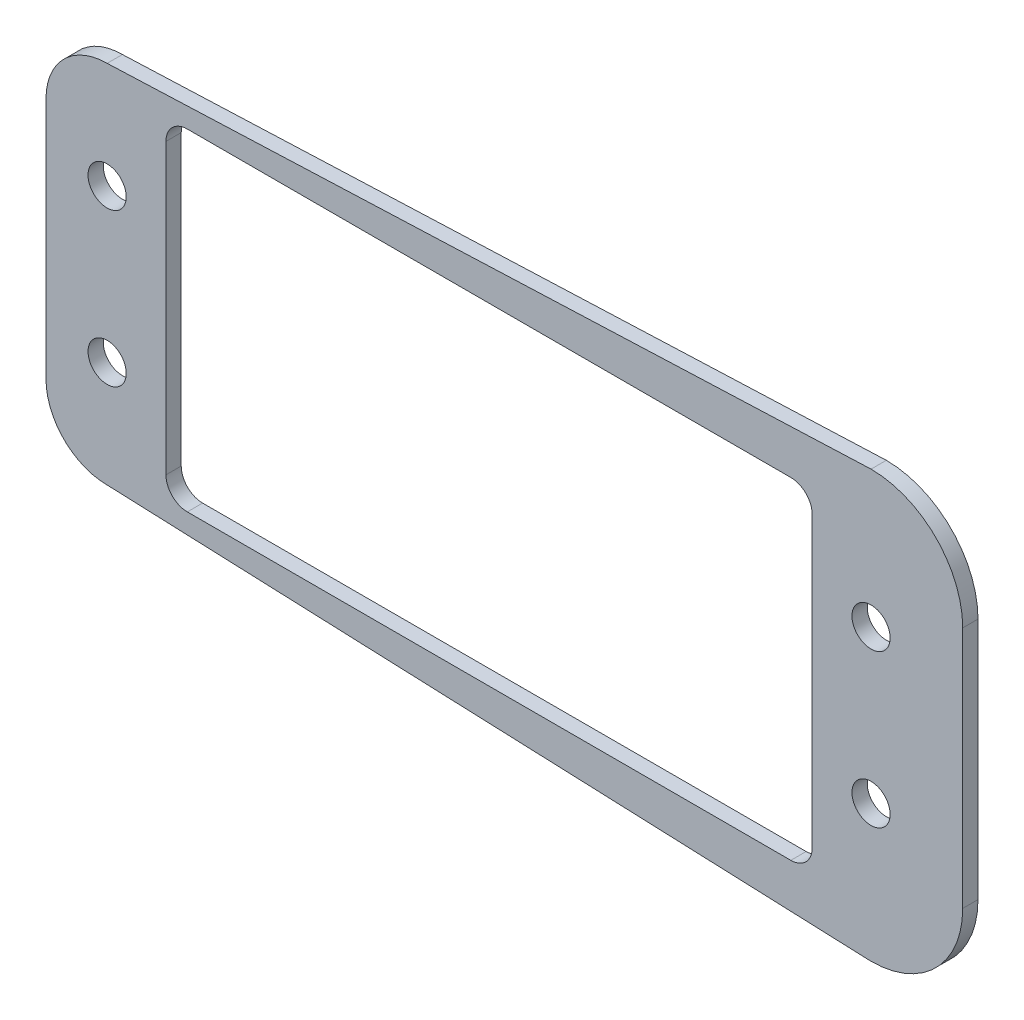
SolidWorks part; units mm, degrees
ref_plane "前视基准面" through (0, 0, 0) normal (0, 0, 1) x (1, 0, 0)
ref_plane "上视基准面" through (0, 0, 0) normal (0, 1, 0) x (1, 0, 0)
ref_plane "右视基准面" through (0, 0, 0) normal (1, 0, 0) x (0, 0, -1)
sketch "草图1" plane through (0, 0, 0) normal (0, 0, 1) x (1, 0, 0)
  line L0 (29.75, 10.85) -> (-9.75, 10.85) construction
  line L1 (41, -7.95) -> (41, 7.95)
  line L2 (29.75, 10.85) -> (-9.75, 10.85)
  line L3 (-19, -7.95) -> (-19, 7.95)
  line L4 (-15, -11.95) -> (35, -13.95)
  line L5 (35, 13.95) -> (-15, 11.95)
  line L6 (-11.15, 9.45) -> (-11.15, -9.45) construction
  line L7 (-11.15, 9.45) -> (-11.15, -9.45)
  line L8 (-9.75, -10.85) -> (29.75, -10.85) construction
  line L9 (-9.75, -10.85) -> (29.75, -10.85)
  line L10 (31.15, -9.45) -> (31.15, 9.45) construction
  line L11 (31.15, -9.45) -> (31.15, 9.45)
  arc A0 (-9.75, 10.85) -> (-11.15, 9.45) centre (-9.75, 9.45) ccw construction
  arc A1 (35, -13.95) -> (41, -7.95) centre (35, -7.95) ccw
  arc A2 (-9.75, 10.85) -> (-11.15, 9.45) centre (-9.75, 9.45) ccw
  arc A3 (41, 7.95) -> (35, 13.95) centre (35, 7.95) ccw
  arc A4 (-11.15, -9.45) -> (-9.75, -10.85) centre (-9.75, -9.45) ccw construction
  arc A5 (-19, -7.95) -> (-15, -11.95) centre (-15, -7.95) ccw
  arc A6 (-11.15, -9.45) -> (-9.75, -10.85) centre (-9.75, -9.45) ccw
  arc A7 (-15, 11.95) -> (-19, 7.95) centre (-15, 7.95) ccw
  arc A8 (31.15, 9.45) -> (29.75, 10.85) centre (29.75, 9.45) ccw construction
  circle A9 centre (35, -5) radius 1.25
  arc A10 (31.15, 9.45) -> (29.75, 10.85) centre (29.75, 9.45) ccw
  circle A11 centre (35, 5) radius 1.25
  arc A12 (29.75, -10.85) -> (31.15, -9.45) centre (29.75, -9.45) ccw construction
  circle A13 centre (-15, -5) radius 1.25
  arc A14 (29.75, -10.85) -> (31.15, -9.45) centre (29.75, -9.45) ccw
  circle A15 centre (-15, 5) radius 1.25
extrude "凸台-拉伸1" add sketch "草图1" along normal blind 1
